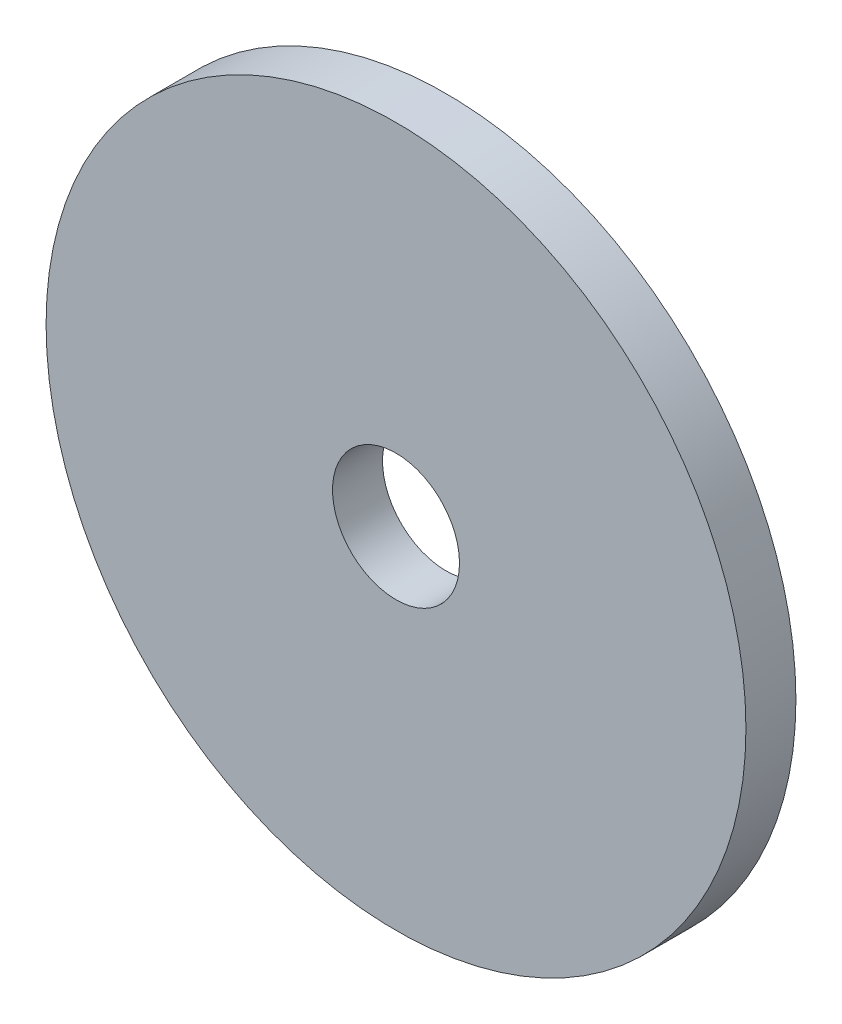
SolidWorks part; units mm, degrees
ref_plane "Front Plane" through (0, 0, 0) normal (0, 0, 1) x (1, 0, 0)
ref_plane "Top Plane" through (0, 0, 0) normal (0, 1, 0) x (1, 0, 0)
ref_plane "Right Plane" through (0, 0, 0) normal (1, 0, 0) x (0, 0, -1)
sketch "Sketch1" plane through (0, 0, 0) normal (0, 0, 1) x (1, 0, 0)
  circle A0 centre (0, 0) radius 140
  circle A1 centre (0, 0) radius 25.4
  dimension "D1" = 280
  dimension "D2" = 50.8
extrude "Boss-Extrude1" add sketch "Sketch1" along normal blind 20
